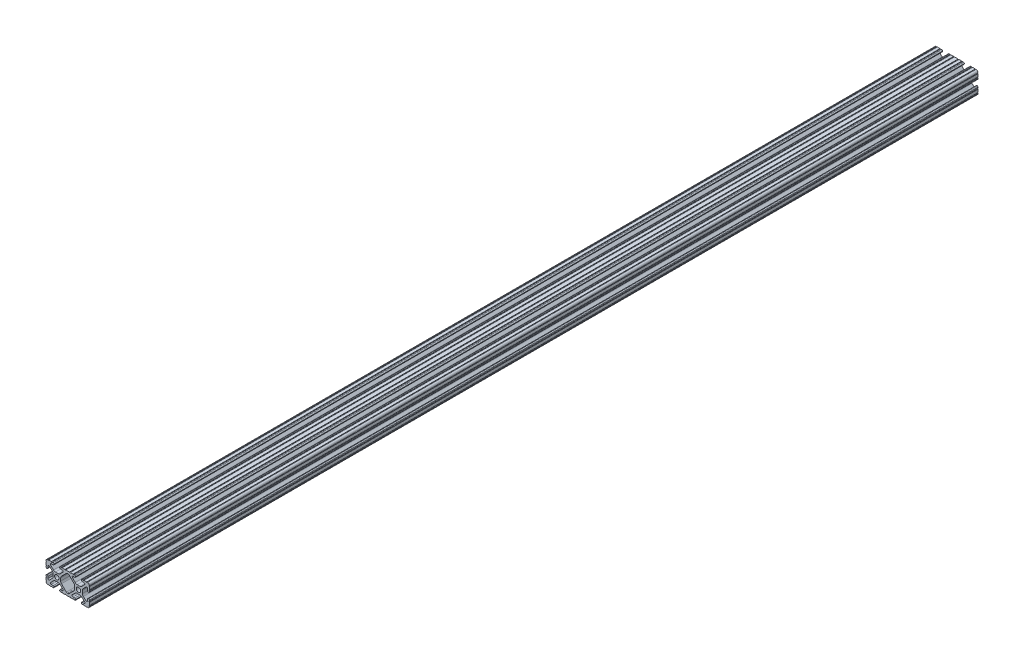
SolidWorks part; units mm, degrees
ref_plane "Front Plane" through (0, 0, 0) normal (0, 0, 1) x (1, 0, 0)
ref_plane "Top Plane" through (0, 0, 0) normal (0, 1, 0) x (1, 0, 0)
ref_plane "Right Plane" through (0, 0, 0) normal (1, 0, 0) x (0, 0, -1)
sketch "Sketch1" plane through (0, 0, 0) normal (0, 0, 1) x (1, 0, 0)
  line L0 (-7.2595, -3.8694) -> (-1.5457, -9.5728)
  line L1 (-8.1915, 1.6223) -> (-8.1915, -1.6223)
  line L2 (-1.504, 9.5765) -> (-7.252, 3.8768)
  line L3 (0.5515, 10.033) -> (-0.3952, 10.033)
  line L4 (7.2829, 3.8459) -> (1.6756, 9.5611)
  line L5 (8.1915, -1.6223) -> (8.1915, 1.6223)
  line L6 (1.5457, -9.5728) -> (7.2595, -3.8694)
  line L7 (-0.4332, -10.033) -> (0.4332, -10.033)
  line L8 (18.0171, 12.7) -> (16.9875, 12.7)
  line L9 (15.9385, 11.651) -> (15.9385, 11.5392)
  line L10 (16.9875, 10.4902) -> (19.1164, 10.4902)
  line L11 (19.8441, 8.7652) -> (16.619, 5.4551)
  line L12 (14.3449, 4.4958) -> (11.0833, 4.4958)
  line L13 (8.817, 5.4472) -> (5.5642, 8.7627)
  line L14 (6.2894, 10.4902) -> (8.4125, 10.4902)
  line L15 (9.4615, 11.5392) -> (9.4615, 11.651)
  line L16 (8.4125, 12.7) -> (7.3829, 12.7)
  line L17 (6.3669, 12.7) -> (3.1496, 12.7)
  line L18 (2.1336, 12.7) -> (-2.1336, 12.7)
  line L19 (-3.1496, 12.7) -> (-6.3669, 12.7)
  line L20 (-7.3829, 12.7) -> (-8.4125, 12.7)
  line L21 (-9.4615, 11.651) -> (-9.4615, 11.5392)
  line L22 (-8.4125, 10.4902) -> (-6.2836, 10.4902)
  line L23 (-5.5326, 8.6661) -> (-8.81, 5.4163)
  line L24 (-11.0455, 4.4958) -> (-14.3545, 4.4958)
  line L25 (-16.59, 5.4163) -> (-19.8674, 8.6661)
  line L26 (-19.1164, 10.4902) -> (-16.9875, 10.4902)
  line L27 (-15.9385, 11.5392) -> (-15.9385, 11.651)
  line L28 (-16.9875, 12.7) -> (-18.0171, 12.7)
  line L29 (-19.0331, 12.7) -> (-22.2504, 12.7)
  line L30 (-25.4, 9.5504) -> (-25.4, 6.3331)
  line L31 (-25.4, 5.3171) -> (-25.4, 4.2375)
  line L32 (-24.401, 3.2385) -> (-24.2392, 3.2385)
  line L33 (-23.1902, 4.2875) -> (-23.1902, 6.3347)
  line L34 (-21.434, 7.0665) -> (-18.148, 3.8082)
  line L35 (-17.2085, 1.5536) -> (-17.2085, -1.6952)
  line L36 (-18.1405, -3.9423) -> (-21.4316, -7.2274)
  line L37 (-23.1902, -6.498) -> (-23.1902, -4.2875)
  line L38 (-24.2392, -3.2385) -> (-24.351, -3.2385)
  line L39 (-25.4, -4.2875) -> (-25.4, -5.3171)
  line L40 (-25.4, -6.3331) -> (-25.4, -9.5504)
  line L41 (-22.2504, -12.7) -> (-19.0331, -12.7)
  line L42 (-18.0171, -12.7) -> (-16.9875, -12.7)
  line L43 (-15.9384, -11.651) -> (-15.9384, -11.5392)
  line L44 (-16.9875, -10.4902) -> (-19.1164, -10.4902)
  line L45 (-19.8341, -8.7551) -> (-16.4966, -5.4237)
  line L46 (-14.2536, -4.4958) -> (-11.1464, -4.4958)
  line L47 (-8.9034, -5.4237) -> (-5.5659, -8.7551)
  line L48 (-6.2836, -10.4902) -> (-8.4125, -10.4902)
  line L49 (-9.4616, -11.5392) -> (-9.4616, -11.651)
  line L50 (-8.4125, -12.7) -> (-7.3829, -12.7)
  line L51 (-6.3669, -12.7) -> (-3.1496, -12.7)
  line L52 (-2.1336, -12.7) -> (2.1336, -12.7)
  line L53 (3.1496, -12.7) -> (6.3669, -12.7)
  line L54 (7.3829, -12.7) -> (8.4125, -12.7)
  line L55 (9.4616, -11.651) -> (9.4616, -11.5392)
  line L56 (8.4125, -10.4902) -> (6.2894, -10.4902)
  line L57 (5.4807, -8.5353) -> (8.5979, -5.4237)
  line L58 (10.8409, -4.4958) -> (14.1026, -4.4958)
  line L59 (16.1879, -5.2766) -> (19.8682, -8.4822)
  line L60 (19.1164, -10.4902) -> (16.9875, -10.4902)
  line L61 (15.9384, -11.5392) -> (15.9384, -11.651)
  line L62 (16.9875, -12.7) -> (18.0171, -12.7)
  line L63 (19.0331, -12.7) -> (22.2504, -12.7)
  line L64 (25.4, -9.5504) -> (25.4, -6.3331)
  line L65 (25.4, -5.3171) -> (25.4, -4.2375)
  line L66 (24.401, -3.2385) -> (24.1892, -3.2385)
  line L67 (23.1902, -4.2375) -> (23.1902, -6.1559)
  line L68 (21.584, -6.8869) -> (18.2982, -4.025)
  line L69 (17.2085, -1.6308) -> (17.2085, 1.6308)
  line L70 (18.1094, 3.8465) -> (21.5263, 7.3534)
  line L71 (23.1902, 6.6769) -> (23.1902, 4.2375)
  line L72 (24.1892, 3.2385) -> (24.401, 3.2385)
  line L73 (25.4, 4.2375) -> (25.4, 5.3171)
  line L74 (25.4, 6.3332) -> (25.4, 9.5504)
  line L75 (22.2504, 12.7) -> (19.0331, 12.7)
  circle A0 centre (-12.7, 0) radius 2.6035
  circle A1 centre (12.7, 0) radius 2.6035
  arc A2 (-1.5457, -9.5728) -> (-0.4332, -10.033) centre (-0.4332, -8.4582) ccw
  arc A3 (-8.1915, -1.6223) -> (-7.2595, -3.8694) centre (-5.0165, -1.6223) ccw
  arc A4 (-7.252, 3.8768) -> (-8.1915, 1.6223) centre (-5.0165, 1.6223) ccw
  arc A5 (-0.3952, 10.033) -> (-1.504, 9.5765) centre (-0.3952, 8.4582) ccw
  arc A6 (1.6756, 9.5611) -> (0.5515, 10.033) centre (0.5515, 8.4582) ccw
  arc A7 (8.1915, 1.6223) -> (7.2829, 3.8459) centre (5.0165, 1.6223) ccw
  arc A8 (7.2595, -3.8694) -> (8.1915, -1.6223) centre (5.0165, -1.6223) ccw
  arc A9 (0.4332, -10.033) -> (1.5457, -9.5728) centre (0.4332, -8.4582) ccw
  arc A10 (18.0171, 12.7) -> (19.0331, 12.7) centre (18.5251, 12.7) ccw
  arc A11 (16.9875, 12.7) -> (15.9385, 11.651) centre (16.9875, 11.651) ccw
  arc A12 (15.9385, 11.5392) -> (16.9875, 10.4902) centre (16.9875, 11.5392) ccw
  arc A13 (19.8441, 8.7652) -> (19.1164, 10.4902) centre (19.1164, 9.4742) ccw
  arc A14 (14.3449, 4.4958) -> (16.619, 5.4551) centre (14.3449, 7.6708) ccw
  arc A15 (8.817, 5.4472) -> (11.0833, 4.4958) centre (11.0833, 7.6708) ccw
  arc A16 (6.2894, 10.4902) -> (5.5642, 8.7627) centre (6.2894, 9.4742) ccw
  arc A17 (8.4125, 10.4902) -> (9.4615, 11.5392) centre (8.4125, 11.5392) ccw
  arc A18 (9.4615, 11.651) -> (8.4125, 12.7) centre (8.4125, 11.651) ccw
  arc A19 (6.3669, 12.7) -> (7.3829, 12.7) centre (6.8749, 12.7) ccw
  arc A20 (2.1336, 12.7) -> (3.1496, 12.7) centre (2.6416, 12.7) ccw
  arc A21 (-3.1496, 12.7) -> (-2.1336, 12.7) centre (-2.6416, 12.7) ccw
  arc A22 (-7.3829, 12.7) -> (-6.3669, 12.7) centre (-6.8749, 12.7) ccw
  arc A23 (-8.4125, 12.7) -> (-9.4615, 11.651) centre (-8.4125, 11.651) ccw
  arc A24 (-9.4615, 11.5392) -> (-8.4125, 10.4902) centre (-8.4125, 11.5392) ccw
  arc A25 (-5.5326, 8.6661) -> (-6.2836, 10.4902) centre (-6.2836, 9.4235) ccw
  arc A26 (-11.0455, 4.4958) -> (-8.81, 5.4163) centre (-11.0455, 7.6708) ccw
  arc A27 (-16.59, 5.4163) -> (-14.3545, 4.4958) centre (-14.3545, 7.6708) ccw
  arc A28 (-19.1164, 10.4902) -> (-19.8674, 8.6661) centre (-19.1164, 9.4235) ccw
  arc A29 (-16.9875, 10.4902) -> (-15.9385, 11.5392) centre (-16.9875, 11.5392) ccw
  arc A30 (-15.9385, 11.651) -> (-16.9875, 12.7) centre (-16.9875, 11.651) ccw
  arc A31 (-19.0331, 12.7) -> (-18.0171, 12.7) centre (-18.5251, 12.7) ccw
  arc A32 (-23.2664, 12.6998) -> (-22.2504, 12.7) centre (-22.7584, 12.7) ccw
  arc A33 (-23.2664, 12.6998) -> (-25.3998, 10.5664) centre (-23.2918, 10.5918) ccw
  arc A34 (-25.4, 9.5504) -> (-25.3998, 10.5664) centre (-25.4, 10.0584) ccw
  arc A35 (-25.4, 5.3171) -> (-25.4, 6.3331) centre (-25.4, 5.8251) ccw
  arc A36 (-25.4, 4.2375) -> (-24.401, 3.2385) centre (-24.401, 4.2375) ccw
  arc A37 (-24.2392, 3.2385) -> (-23.1902, 4.2875) centre (-24.2392, 4.2875) ccw
  arc A38 (-21.434, 7.0665) -> (-23.1902, 6.3347) centre (-22.1596, 6.3347) ccw
  arc A39 (-17.2085, 1.5536) -> (-18.148, 3.8082) centre (-20.3835, 1.5536) ccw
  arc A40 (-18.1405, -3.9423) -> (-17.2085, -1.6952) centre (-20.3835, -1.6952) ccw
  arc A41 (-23.1902, -6.498) -> (-21.4316, -7.2274) centre (-22.1596, -6.498) ccw
  arc A42 (-23.1902, -4.2875) -> (-24.2392, -3.2385) centre (-24.2392, -4.2875) ccw
  arc A43 (-24.351, -3.2385) -> (-25.4, -4.2875) centre (-24.351, -4.2875) ccw
  arc A44 (-25.4, -6.3331) -> (-25.4, -5.3171) centre (-25.4, -5.8251) ccw
  arc A45 (-25.3998, -10.5664) -> (-25.4, -9.5504) centre (-25.4, -10.0584) ccw
  arc A46 (-25.3998, -10.5664) -> (-23.2664, -12.6998) centre (-23.2918, -10.5918) ccw
  arc A47 (-22.2504, -12.7) -> (-23.2664, -12.6998) centre (-22.7584, -12.7) ccw
  arc A48 (-18.0171, -12.7) -> (-19.0331, -12.7) centre (-18.5251, -12.7) ccw
  arc A49 (-16.9875, -12.7) -> (-15.9384, -11.651) centre (-16.9875, -11.651) ccw
  arc A50 (-15.9384, -11.5392) -> (-16.9875, -10.4902) centre (-16.9875, -11.5392) ccw
  arc A51 (-19.8341, -8.7551) -> (-19.1164, -10.4902) centre (-19.1164, -9.4742) ccw
  arc A52 (-14.2536, -4.4958) -> (-16.4966, -5.4237) centre (-14.2536, -7.6708) ccw
  arc A53 (-8.9034, -5.4237) -> (-11.1464, -4.4958) centre (-11.1464, -7.6708) ccw
  arc A54 (-6.2836, -10.4902) -> (-5.5659, -8.7551) centre (-6.2836, -9.4742) ccw
  arc A55 (-8.4125, -10.4902) -> (-9.4616, -11.5392) centre (-8.4125, -11.5392) ccw
  arc A56 (-9.4616, -11.651) -> (-8.4125, -12.7) centre (-8.4125, -11.651) ccw
  arc A57 (-6.3669, -12.7) -> (-7.3829, -12.7) centre (-6.8749, -12.7) ccw
  arc A58 (-2.1336, -12.7) -> (-3.1496, -12.7) centre (-2.6416, -12.7) ccw
  arc A59 (3.1496, -12.7) -> (2.1336, -12.7) centre (2.6416, -12.7) ccw
  arc A60 (7.3829, -12.7) -> (6.3669, -12.7) centre (6.8749, -12.7) ccw
  arc A61 (8.4125, -12.7) -> (9.4616, -11.651) centre (8.4125, -11.651) ccw
  arc A62 (9.4616, -11.5392) -> (8.4125, -10.4902) centre (8.4125, -11.5392) ccw
  arc A63 (5.4807, -8.5353) -> (6.2894, -10.4902) centre (6.2894, -9.3455) ccw
  arc A64 (10.8409, -4.4958) -> (8.5979, -5.4237) centre (10.8409, -7.6708) ccw
  arc A65 (16.1879, -5.2766) -> (14.1026, -4.4958) centre (14.1026, -7.6708) ccw
  arc A66 (19.1164, -10.4902) -> (19.8682, -8.4822) centre (19.1164, -9.3455) ccw
  arc A67 (16.9875, -10.4902) -> (15.9384, -11.5392) centre (16.9875, -11.5392) ccw
  arc A68 (15.9384, -11.651) -> (16.9875, -12.7) centre (16.9875, -11.651) ccw
  arc A69 (19.0331, -12.7) -> (18.0171, -12.7) centre (18.5251, -12.7) ccw
  arc A70 (23.2664, -12.6998) -> (22.2504, -12.7) centre (22.7584, -12.7) ccw
  arc A71 (23.2664, -12.6998) -> (25.3998, -10.5664) centre (23.2918, -10.5918) ccw
  arc A72 (25.4, -9.5504) -> (25.3998, -10.5664) centre (25.4, -10.0584) ccw
  arc A73 (25.4, -5.3171) -> (25.4, -6.3331) centre (25.4, -5.8251) ccw
  arc A74 (25.4, -4.2375) -> (24.401, -3.2385) centre (24.401, -4.2375) ccw
  arc A75 (24.1892, -3.2385) -> (23.1902, -4.2375) centre (24.1892, -4.2375) ccw
  arc A76 (21.584, -6.8869) -> (23.1902, -6.1559) centre (22.2207, -6.1559) ccw
  arc A77 (17.2085, -1.6308) -> (18.2982, -4.025) centre (20.3835, -1.6308) ccw
  arc A78 (18.1094, 3.8465) -> (17.2085, 1.6308) centre (20.3835, 1.6308) ccw
  arc A79 (23.1902, 6.6769) -> (21.5263, 7.3534) centre (22.2207, 6.6769) ccw
  arc A80 (23.1902, 4.2375) -> (24.1892, 3.2385) centre (24.1892, 4.2375) ccw
  arc A81 (24.401, 3.2385) -> (25.4, 4.2375) centre (24.401, 4.2375) ccw
  arc A82 (25.4, 6.3332) -> (25.4, 5.3171) centre (25.4, 5.8251) ccw
  arc A83 (25.3998, 10.5664) -> (25.4, 9.5504) centre (25.4, 10.0584) ccw
  arc A84 (25.3998, 10.5664) -> (23.2664, 12.6998) centre (23.2918, 10.5918) ccw
  arc A85 (22.2504, 12.7) -> (23.2664, 12.6998) centre (22.7584, 12.7) ccw
  point P248 (0, 10.033)
extrude "Boss-Extrude1" add sketch "Sketch1" along normal mid plane 1041.4
